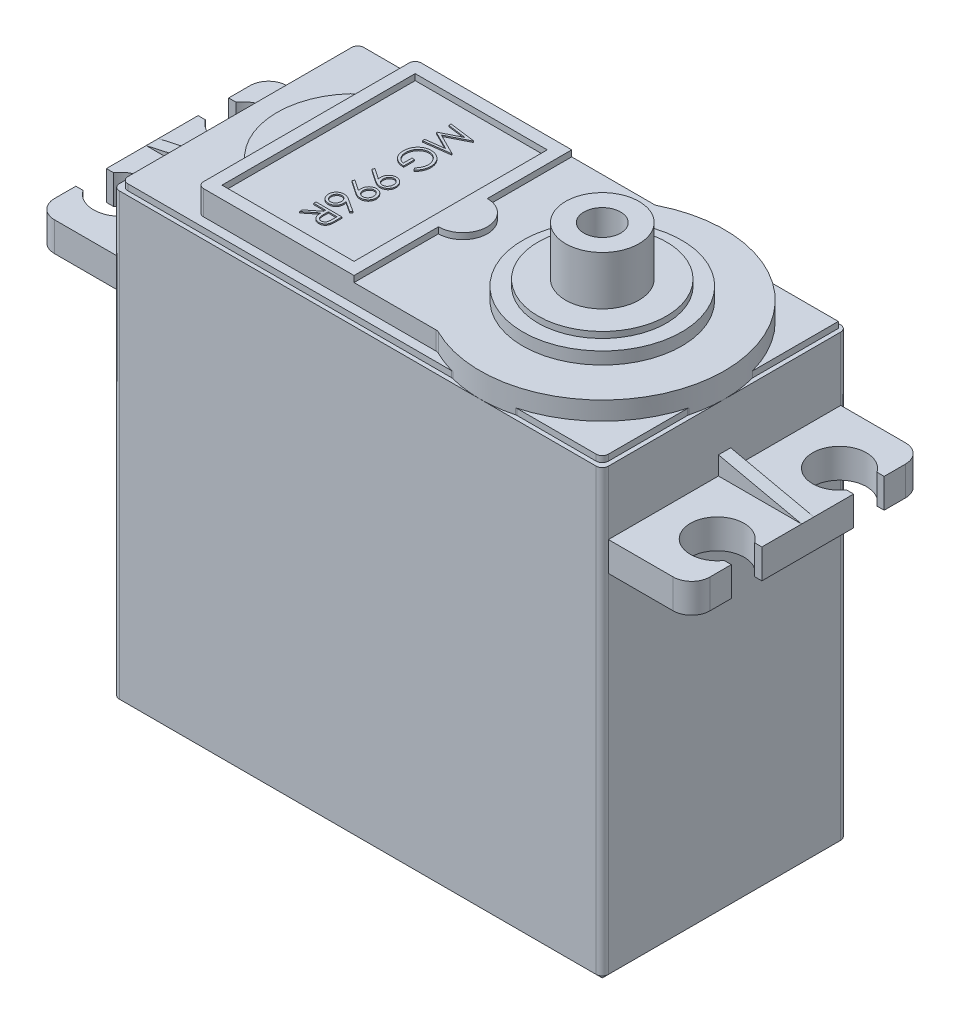
SolidWorks part; units mm, degrees
ref_plane "Front Plane" through (0, 0, 0) normal (0, 0, 1) x (1, 0, 0)
ref_plane "Top Plane" through (0, 0, 0) normal (0, 1, 0) x (1, 0, 0)
ref_plane "Right Plane" through (0, 0, 0) normal (1, 0, 0) x (0, 0, -1)
sketch "Sketch2" plane through (0, 0, 0) normal (0, 1, 0) x (1, 0, 0)
  line L1 (-20, 10) -> (20, 10)
  line L2 (-20, 10) -> (-20, -10)
  line L3 (-20, -10) -> (20, -10)
  line L4 (20, 10) -> (20, -10)
  line L5 (-20, 10) -> (20, -10) construction
  line L6 (-20, -10) -> (20, 10) construction
  point P0 (0, 0)
  dimension "D1" = 40
  dimension "0" = 20
extrude "Boss-Extrude1" add sketch "Sketch2" along normal blind 38
sketch "Sketch3" plane through (0, 38, 0) normal (0, 1, 0) x (1, 0, 0)
  line L0 (0, 0) -> (20, 0) construction
  line L1 (20, -10) -> (20, 10) construction
  line L2 (20, 10) -> (-20, 10) construction
  line L3 (0, 0) -> (-20, 0) construction
  line L4 (-20, 10) -> (-20, -10) construction
  line L6 (-14.2, -8.9) -> (5.4404, -8.9)
  line L7 (-14.2, -8.9) -> (-14.2, 8.9)
  line L8 (-14.2, 8.9) -> (5.4404, 8.9)
  line L9 (5.4404, -8.9) -> (5.4404, 8.9)
  line L10 (-14.2, -8.9) -> (5.4404, 8.9) construction
  line L11 (-14.2, 8.9) -> (5.4404, -8.9) construction
  circle A0 centre (10, 0) radius 10
  circle A1 centre (-10.1917, 0) radius 6.4083
  point P12 (-4.3798, 0)
  point P17 (-16.6, 0)
  point P21 (-14.2, 5)
  dimension "D1" = 5.8
  dimension "D2" = 17.8
  dimension "D3" = 3.4
  dimension "D4" = 5
extrude "Boss-Extrude2" add sketch "Sketch3" along normal blind 2 contours A0 L9 | L9 A0 | A1 L7 L6 A0 L8 | L7 A1 | L7 A1
sketch "Sketch4" plane through (0, 38, 0) normal (0, 1, 0) x (1, 0, 0)
  line L14 (-19.65, 9.65) -> (-19.65, -9.65)
  line L15 (-19.65, -9.65) -> (10, -9.65)
  line L16 (10, -9.65) -> (19.65, -9.65)
  line L17 (19.65, -9.65) -> (19.65, 0)
  line L18 (19.65, 0) -> (19.65, 9.65)
  line L19 (19.65, 9.65) -> (10, 9.65)
  line L20 (10, 9.65) -> (-19.65, 9.65)
  line L21 (-19.65, 9.65) -> (-19.65, -9.65)
  line L22 (-19.65, -9.65) -> (10, -9.65)
  line L23 (10, -9.65) -> (19.65, -9.65)
  line L24 (19.65, -9.65) -> (19.65, 0)
  line L25 (19.65, 0) -> (19.65, 9.65)
  line L26 (19.65, 9.65) -> (10, 9.65)
  line L27 (10, 9.65) -> (-19.65, 9.65)
  dimension "D1" = 0.35
extrude "Boss-Extrude3" add sketch "Sketch4" along normal blind 0.5
sketch "Sketch5" plane through (0, 40, 0) normal (0, 1, 0) x (1, 0, 0)
  line L0 (-14.2, -8.9) -> (5.4404, -8.9) construction
  line L1 (-14.2, 8.9) -> (-1.4, 8.9)
  line L2 (-14.2, 8.9) -> (-14.2, -8.9)
  line L3 (-14.2, -8.9) -> (-1.4, -8.9)
  line L4 (-1.4, 8.9) -> (-1.4, -8.9)
  line L5 (-14.2, 8.9) -> (-1.4, -8.9) construction
  line L7 (-13.2, -7.9) -> (-2.4, -7.9)
  line L8 (-13.2, -7.9) -> (-13.2, 7.9)
  line L9 (-13.2, 7.9) -> (-2.4, 7.9)
  line L10 (-2.4, -7.9) -> (-2.4, 7.9)
  line L11 (-13.2, -7.9) -> (-2.4, 7.9) construction
  line L12 (-13.2, 7.9) -> (-2.4, -7.9) construction
  point P7 (-7.8, 0)
  dimension "D1" = 12.8
  dimension "D2" = 1
  dimension "D3" = 1
extrude "Boss-Extrude4" add sketch "Sketch5" along normal blind 0.5
sketch "Sketch6" plane through (0, 40, 0) normal (0, 1, 0) x (1, 0, 0)
  line L0 (0, 0) -> (-19.65, 0) construction
  line L1 (-19.65, 9.65) -> (-19.65, -9.65) construction
  line L2 (-1.4, -8.9) -> (-1.4, 8.9) construction
  line L3 (-1.4, 2) -> (-1.4, -2)
  circle A0 centre (-1.4, 0) radius 2
  dimension "D1" = 4
extrude "Boss-Extrude5" add sketch "Sketch6" along normal blind 0.5
sketch "Sketch7" plane through (0, 40, 0) normal (0, 1, 0) x (1, 0, 0)
  circle A0 centre (10, 0) radius 6.5
  dimension "D1" = 13
extrude "Boss-Extrude6" add sketch "Sketch7" along normal blind 1
sketch "Sketch8" plane through (0, 41, 0) normal (0, 1, 0) x (1, 0, 0)
  circle A0 centre (10, 0) radius 5.25
  dimension "D1" = 10.5
extrude "Boss-Extrude7" add sketch "Sketch8" along normal blind 0.5
sketch "Sketch9" plane through (0, 41.5, 0) normal (0, 1, 0) x (1, 0, 0)
  circle A0 centre (10, 0) radius 3
  dimension "D1" = 6
extrude "Boss-Extrude8" add sketch "Sketch9" along normal blind 4
sketch "Sketch10" plane through (0, 45.5, 0) normal (0, 1, 0) x (1, 0, 0)
  circle A0 centre (10, 0) radius 1.5
  dimension "D1" = 3
extrude "Cut-Extrude1" cut sketch "Sketch10" against normal blind 10
chamfer "Chamfer1" distance 2 angle 45 4 edges at (20, 0, 0) (0, 0, -10) (-20, 0, 0) (0, 0, 10)
sketch "Sketch11" plane through (0, 0, 0) normal (0, -1, 0) x (1, 0, 0)
  line L0 (0, 0) -> (0, 10) construction
  line L1 (-20, 10) -> (20, 10) construction
  line L2 (0, 0) -> (20, 0) construction
  circle A0 centre (-20, 10) radius 2.8284
  circle A1 centre (20, 10) radius 2.8284
  circle A2 centre (20, -10) radius 2.8284
  circle A3 centre (-20, -10) radius 2.8284
extrude "Cut-Extrude2" cut sketch "Sketch11" against normal blind 2
ref_plane "Plane4" through (0, 32.8, 0) normal (0, 1, 0) x (1, 0, 0)
fillet "Fillet1" radius 0.5 4 edges at (-20, 20, -10) (-20, 20, 10) (20, 20, -10) (20, 20, 10)
fillet "Fillet2" radius 0.5 13 edges at (5.4404, 39.25, -8.9) (-14.2, 39.5, -8.9) (-14.2, 39.25, -5) (-14.2, 39.25, 5) (-14.2, 39.5, 8.9) (-19.65, 38.25, 9.65) (-19.65, 38.25, -9.65) (7.3775, 38.25, -9.65) (5.4404, 39.25, 8.9) (12.6225, 38.25, 9.65) (7.3775, 38.25, 9.65) (19.65, 38.25, 2.6225) (19.65, 38.25, 9.65)
sketch "Sketch13" plane through (0, 32.8, 0) normal (0, 1, 0) x (1, 0, 0)
  line L0 (26.8, 0) -> (20, 0) construction
  line L1 (20, 9.5) -> (26.8, 9.5)
  line L2 (20, 9.5) -> (20, -9.5)
  line L3 (20, -9.5) -> (26.8, -9.5)
  line L4 (26.8, 9.5) -> (26.8, -9.5)
  line L5 (24.4, -5) -> (24.4, 5)
  line L6 (24.4, 5) -> (26.8, 5) construction
  line L7 (29.2, -6.25) -> (24.4, -6.25)
  line L8 (29.2, 3.75) -> (24.4, 3.75)
  line L9 (29.2, 3.75) -> (29.2, 6.25)
  line L10 (29.2, 6.25) -> (24.4, 6.25)
  line L11 (24.4, 3.75) -> (24.4, 6.25)
  line L12 (29.2, 3.75) -> (24.4, 6.25) construction
  line L13 (29.2, 6.25) -> (24.4, 3.75) construction
  line L14 (24.4, -3.75) -> (24.4, -6.25)
  line L15 (29.2, -3.75) -> (24.4, -3.75)
  line L16 (29.2, -3.75) -> (29.2, -6.25)
  line L17 (0, 0) -> (0, 10) construction
  line L18 (10, 10) -> (-19.5, 10) construction
  line L19 (-29.2, 6.25) -> (-24.4, 3.75) construction
  line L20 (-29.2, 3.75) -> (-24.4, 6.25) construction
  line L21 (-24.4, 5) -> (-26.8, 5) construction
  line L22 (-26.8, 0) -> (-20, 0) construction
  line L23 (-29.2, -3.75) -> (-29.2, -6.25)
  line L24 (-29.2, -3.75) -> (-24.4, -3.75)
  line L25 (-24.4, -3.75) -> (-24.4, -6.25)
  line L26 (-24.4, 3.75) -> (-24.4, 6.25)
  line L27 (-29.2, 6.25) -> (-24.4, 6.25)
  line L28 (-29.2, 3.75) -> (-29.2, 6.25)
  line L29 (-29.2, 3.75) -> (-24.4, 3.75)
  line L30 (-29.2, -6.25) -> (-24.4, -6.25)
  line L31 (-24.4, -5) -> (-24.4, 5)
  line L32 (-26.8, 9.5) -> (-26.8, -9.5)
  line L33 (-20, -9.5) -> (-26.8, -9.5)
  line L34 (-20, 9.5) -> (-20, -9.5)
  line L35 (-20, 9.5) -> (-26.8, 9.5)
  circle A0 centre (24.4, 5) radius 2.2
  circle A1 centre (24.4, -5) radius 2.2
  circle A2 centre (-24.4, -5) radius 2.2
  circle A3 centre (-24.4, 5) radius 2.2
  point P11 (24.4, 0)
  point P46 (-24.4, 0)
  dimension "D3" = 4.4
  dimension "D1" = 6.8
  dimension "D2" = 10
  dimension "D4" = 2.4
  dimension "D5" = 2.5
extrude "Boss-Extrude9" add sketch "Sketch13" against normal blind 2.4 contours L27 A3 L31 A2 L30 L32 L33 L34 L35 | L31 A3 L29 L32 L24 A2 | A1 L5 A0 L10 L4 L1 L2 L3 L7 | A1 L15 L4 L8 A0 L5
sketch "Sketch14" plane through (0, 0, 0) normal (0, 0, 1) x (1, 0, 0)
  line L0 (20, 34.3) -> (26.8, 32.8)
  line L1 (20, 38) -> (20, 32.8) construction
  line L2 (20, 32.8) -> (26.8, 32.8) construction
  line L3 (20, 34.3) -> (20, 32.8)
  line L4 (20, 32.8) -> (26.8, 32.8)
  line L5 (0, 0) -> (0, 36.6111) construction
  line L6 (-20, 32.8) -> (-26.8, 32.8)
  line L7 (-20, 34.3) -> (-20, 32.8)
  line L8 (-20, 34.3) -> (-26.8, 32.8)
  dimension "D1" = 1.5
extrude "Boss-Extrude10" add sketch "Sketch14" along normal blind 0.5 and the other way blind 0.5
sketch "Sketch15" plane through (0, 40, 0) normal (0, 1, 0) x (1, 0, 0)
  line L0 (-8.5615, 7.9) -> (-8.5615, -7.9) construction
  line L1 (-2.4, 7.9) -> (-13.2, 7.9) construction
  line L2 (-13.2, -7.9) -> (-2.4, -7.9) construction
  text T0 "MG 996R" font "Century Gothic" height in points 8
extrude "Boss-Extrude11" add sketch "Sketch15" along normal blind 0.1
fillet "Fillet3" radius 1.5 4 edges at (-26.8, 31.6, -9.5) (-26.8, 31.6, 9.5) (26.8, 31.6, -9.5) (26.8, 31.6, 9.5)
